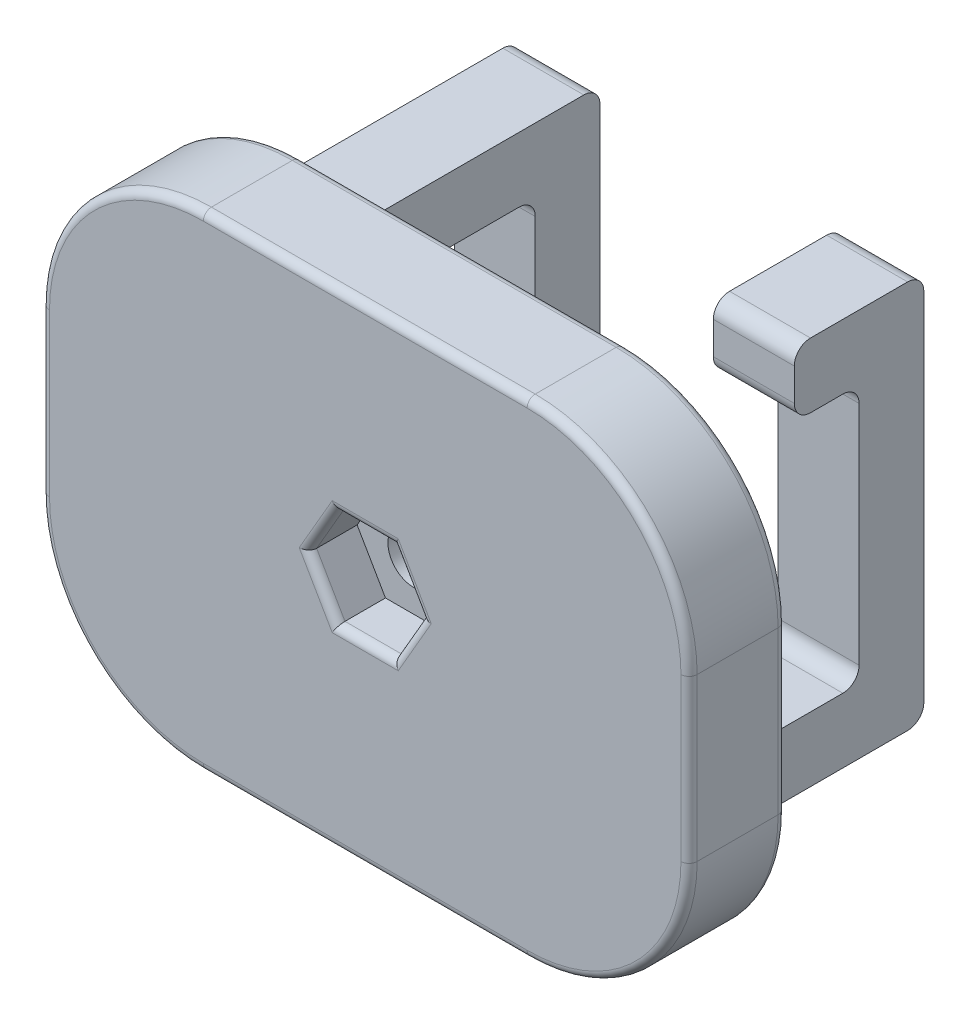
SolidWorks part; units mm, degrees
ref_plane "Front Plane" through (0, 0, 0) normal (0, 0, 1) x (1, 0, 0)
ref_plane "Top Plane" through (0, 0, 0) normal (0, 1, 0) x (1, 0, 0)
ref_plane "Right Plane" through (0, 0, 0) normal (1, 0, 0) x (0, 0, -1)
sketch "Sketch1" plane through (0, 0, 0) normal (0, 1, 0) x (1, 0, 0)
  line L0 (-8, 0) -> (8, 0)
  line L1 (8, 0) -> (8, 3.6)
  line L2 (8, 3.6) -> (4.3, 7.2)
  line L3 (4.3, 7.2) -> (-4.3, 7.2)
  line L4 (-4.3, 7.2) -> (-8, 3.6)
  line L5 (-8, 3.6) -> (-8, 0)
  point P4 (0, 0)
  dimension "D1" = 16
  dimension "D2" = 8.6
  dimension "D3" = 7.2
  dimension "D4" = 3.6
extrude "Boss-Extrude1" add sketch "Sketch1" along normal mid plane 12
sketch "Sketch2" plane through (0, 0, -7.2) normal (0, 0, -1) x (-1, 0, 0)
  line L1 (-3.8, -4.2) -> (3.8, -4.2)
  line L2 (-3.8, -4.2) -> (-3.8, 4.2)
  line L3 (-3.8, 4.2) -> (3.8, 4.2)
  line L4 (3.8, -4.2) -> (3.8, 4.2)
  line L5 (-3.8, -4.2) -> (3.8, 4.2) construction
  line L6 (-3.8, 4.2) -> (3.8, -4.2) construction
  point P0 (0, 0)
  dimension "D1" = 7.6
  dimension "D2" = 8.4
extrude "Boss-Extrude2" add sketch "Sketch2" along normal blind 4
sketch "Sketch3" plane through (0, 0, -11.2) normal (0, 0, -1) x (-1, 0, 0)
  line L1 (-20, -15) -> (20, -15)
  line L2 (-20, -15) -> (-20, 15)
  line L3 (-20, 15) -> (20, 15)
  line L4 (20, -15) -> (20, 15)
  line L5 (-20, -15) -> (20, 15) construction
  line L6 (-20, 15) -> (20, -15) construction
  point P0 (0, 0)
  dimension "D1" = 30
  dimension "D2" = 40
extrude "Boss-Extrude3" add sketch "Sketch3" along normal blind 6
ref_plane "Plane1" through (-10, 0, 0) normal (-1, 0, 0) x (0, 0, 1)
sketch "Sketch6" plane through (-10, 0, 0) normal (-1, 0, 0) x (0, 0, 1)
  line L0 (-17.2, 12) -> (-33.2, 12)
  line L1 (-33.2, 12) -> (-33.2, -12)
  line L2 (-33.2, -12) -> (-25.2, -12)
  line L3 (-25.2, -12) -> (-25.2, -8)
  line L4 (-25.2, -8) -> (-29.2, -8)
  line L5 (-29.2, -8) -> (-29.2, 8)
  line L6 (-29.2, 8) -> (-17.2, 8)
  line L7 (-17.2, 8) -> (-17.2, 12)
  line L8 (-17.2, -15) -> (-17.2, 15) construction
  line L9 (-17.2, -15) -> (-17.2, 15)
  line L10 (-17.2, 15) -> (-11.2, 15) construction
  line L11 (-17.2, -15) -> (-11.2, -15) construction
  dimension "D1" = 4
  dimension "D2" = 4
  dimension "D3" = 4
  dimension "D4" = 8
  dimension "D5" = 4
  dimension "D6" = 3
  dimension "D7" = 3
extrude "Boss-Extrude4" add sketch "Sketch6" along normal mid plane 5 contours L6 L7 L0 L1 L2 L3 L4 L5
ref_plane "Plane2" through (10, 0, 0) normal (1, 0, 0) x (0, 0, -1)
sketch "Sketch7" plane through (10, 0, 0) normal (1, 0, 0) x (0, 0, -1)
  line L0 (25.2, 8) -> (25.2, 12)
  line L1 (17.2, 15) -> (17.2, -15) construction
  line L2 (17.2, 15) -> (17.2, -15)
  line L3 (17.2, -12) -> (17.2, -8)
  line L4 (17.2, -8) -> (29.2, -8)
  line L5 (29.2, 8) -> (25.2, 8)
  line L6 (25.2, 12) -> (33.2, 12)
  line L7 (33.2, -12) -> (17.2, -12)
  line L8 (17.2, 8) -> (29.2, 8)
  line L9 (29.2, 8) -> (29.2, -8)
  line L10 (29.2, -8) -> (25.2, -8)
  line L11 (25.2, -8) -> (25.2, -12)
  line L12 (25.2, -12) -> (33.2, -12)
  line L13 (33.2, -12) -> (33.2, 12)
  line L14 (33.2, 12) -> (17.2, 12)
  line L15 (17.2, 12) -> (17.2, 8)
  line L16 (25.2, 8) -> (29.2, 8)
  line L17 (29.2, 8) -> (29.2, -8)
  line L18 (29.2, -8) -> (17.2, -8)
  line L20 (17.2, -12) -> (33.2, -12)
  line L21 (33.2, -12) -> (33.2, 12)
  line L22 (33.2, 12) -> (25.2, 12)
  line L23 (17.2, 12) -> (17.2, 8)
  dimension "D2" = 4
  dimension "D1" = 0
extrude "Boss-Extrude5" add sketch "Sketch7" along normal mid plane 5 contours L7 L21 L6 L0 L5 L17 L4 L2
fillet "Fillet1" radius 10 4 edges at (-20, -15, -14.2) (-20, 15, -14.2) (20, -15, -14.2) (20, 15, -14.2)
sketch "Sketch8" plane through (0, 0, 0) normal (0, 0, 1) x (1, 0, 0)
  circle A0 centre (0, 0) radius 1.6
  dimension "D1" = 3.2
extrude "Cut-Extrude1" cut sketch "Sketch8" against normal through all
fillet "Fillet3" radius 0.5 12 edges at (8, 6, -1.8) (0, 6, 0) (-8, 6, -1.8) (-6.15, 6, -5.4) (0, 6, -7.2) (6.15, 6, -5.4) (0, -6, -7.2) (-6.15, -6, -5.4) (-8, -6, -1.8) (0, -6, 0) (8, -6, -1.8) (6.15, -6, -5.4)
fillet "Fillet4" radius 0.5 16 edges at (20, 0, -11.2) (17.0711, -12.0711, -11.2) (0, -15, -11.2) (-17.0711, -12.0711, -11.2) (-20, 0, -11.2) (-17.0711, 12.0711, -11.2) (0, 15, -11.2) (0, 15, -17.2) (-17.0711, 12.0711, -17.2) (-20, 0, -17.2) (-17.0711, -12.0711, -17.2) (0, -15, -17.2) (17.0711, -12.0711, -17.2) (20, 0, -17.2) (17.0711, 12.0711, -11.2) (17.0711, 12.0711, -17.2)
fillet "Fillet5" radius 0.5 4 edges at (0, -4.2, -11.2) (3.8, 0, -11.2) (0, 4.2, -11.2) (-3.8, 0, -11.2)
sketch "Sketch9" plane through (0, 0, -11.2) normal (0, 0, 1) x (1, 0, 0)
  circle A0 centre (0, 0) radius 14.3295
  point P3 (0, 0)
extrude "Cut-Extrude2" cut sketch "Sketch9" along normal through all
sketch "Sketch10" plane through (0, 0, -11.2) normal (0, 0, 1) x (1, 0, 0)
  line L1 (3.5, 0) -> (1.75, 3.0311)
  line L2 (1.75, 3.0311) -> (-1.75, 3.0311)
  line L3 (-1.75, 3.0311) -> (-3.5, 0)
  line L4 (-3.5, 0) -> (-1.75, -3.0311)
  line L5 (-1.75, -3.0311) -> (1.75, -3.0311)
  line L6 (1.75, -3.0311) -> (3.5, 0)
  circle A0 centre (0, 0) radius 3.5 construction
  circle A1 centre (0, 0) radius 3.0311 construction
  dimension "D1" = 7
extrude "Cut-Extrude3" cut sketch "Sketch10" against normal blind 3
fillet "Fillet6" radius 0.5 6 edges at (0, -3.0311, -11.2) (2.625, -1.5155, -11.2) (2.625, 1.5155, -11.2) (0, 3.0311, -11.2) (-2.625, 1.5155, -11.2) (-2.625, -1.5155, -11.2)
fillet "Fillet7" radius 1 12 edges at (10, 8, -29.2) (-10, 8, -29.2) (-10, -12, -25.2) (-10, -8, -25.2) (10, 8, -25.2) (10, 12, -25.2) (10, -8, -29.2) (-10, -8, -29.2) (-10, -12, -33.2) (10, 12, -33.2) (-10, 12, -33.2) (10, -12, -33.2)
fillet "Fillet8" radius 1.5 8 edges at (-7.5, 10, -17.2) (-10, 8, -17.2) (10, -12, -17.2) (-10, 12, -17.2) (-12.5, 10, -17.2) (7.5, -10, -17.2) (10, -8, -17.2) (12.5, -10, -17.2)
fillet "Fillet9" radius 0.3 1 edges at (1.6, 0, -17.2)
